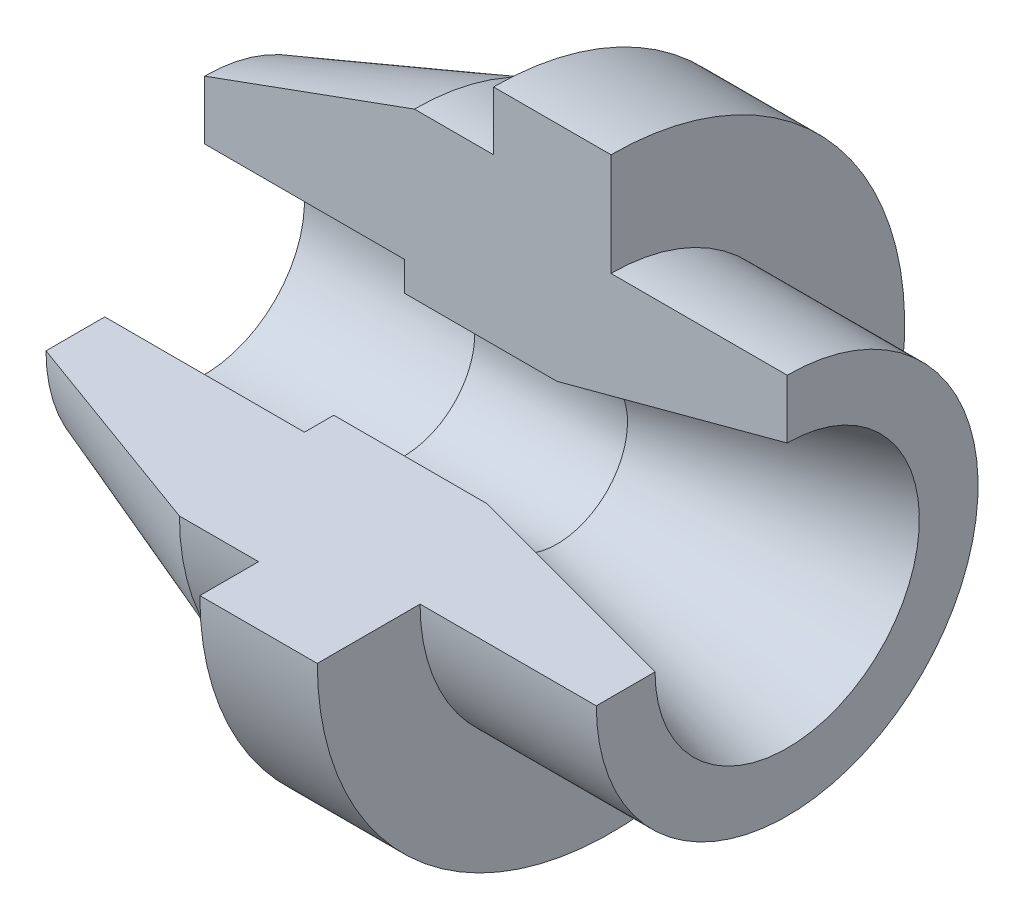
SolidWorks part; units mm, degrees
ref_plane "Front Plane" through (0, 0, 0) normal (0, 0, 1) x (1, 0, 0)
ref_plane "Top Plane" through (0, 0, 0) normal (0, 1, 0) x (1, 0, 0)
ref_plane "Right Plane" through (0, 0, 0) normal (1, 0, 0) x (0, 0, -1)
sketch "Sketch1" plane through (0, 0, 0) normal (0, 1, 0) x (1, 0, 0)
  line L0 (0, 0) -> (78.9727, 0) construction
  line L1 (0, -17) -> (0, -27)
  line L2 (0, -27) -> (35.7172, -40)
  line L3 (35.7172, -40) -> (49.1865, -40)
  line L4 (49.1865, -40) -> (49.1865, -50)
  line L5 (49.1865, -50) -> (69.1865, -50)
  line L6 (69.1865, -50) -> (69.1865, -32.5)
  line L7 (69.1865, -32.5) -> (99.1865, -32.5)
  line L8 (99.1865, -32.5) -> (99.1865, -22.5)
  line L9 (99.1865, -22.5) -> (60, -12)
  line L10 (60, -12) -> (34, -12)
  line L11 (34, -12) -> (34, -17)
  line L12 (34, -17) -> (0, -17)
  dimension "D1" = 60
  dimension "D2" = 10
  dimension "D3" = 30
  dimension "D4" = 40
  dimension "D5" = 27
  dimension "D6" = 17
  dimension "D7" = 12
  dimension "D8" = 32.5
  dimension "D9" = 50
  dimension "D10" = 34
  dimension "D11" = 70
  dimension "D12" = 20
  dimension "D13" = 15
revolve "Revolve1" add sketch "Sketch1" angle 270 about L0
